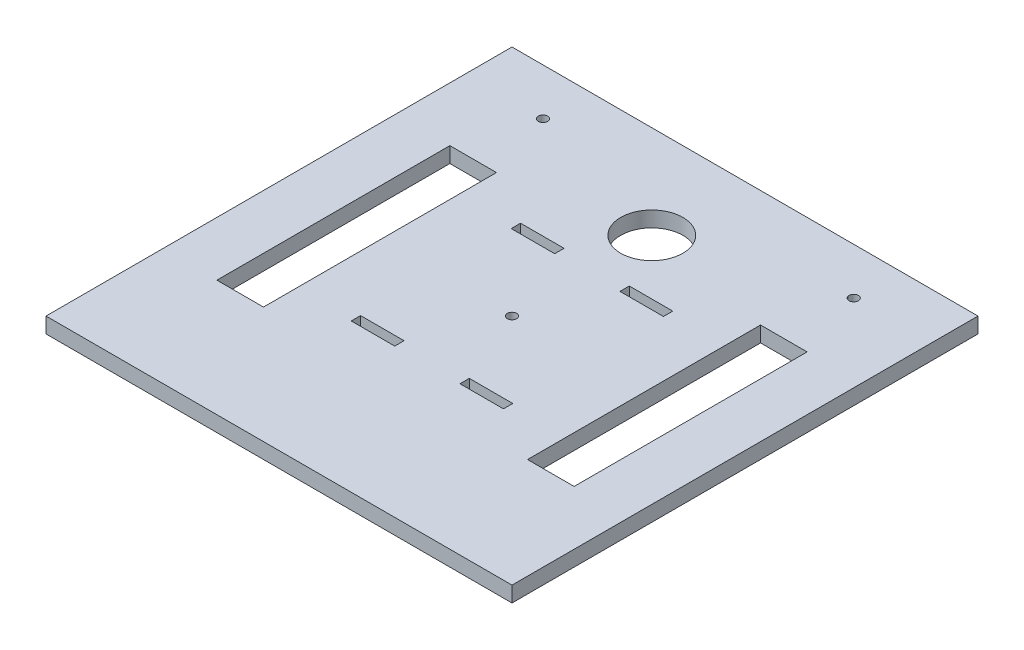
SolidWorks part; units mm, degrees
ref_plane "Front" through (0, 0, 0) normal (0, 0, 1) x (1, 0, 0)
ref_plane "Top" through (0, 0, 0) normal (0, 1, 0) x (1, 0, 0)
ref_plane "Right" through (0, 0, 0) normal (1, 0, 0) x (0, 0, -1)
sketch "Sketch1" plane through (0, 0, 0) normal (0, 1, 0) x (1, 0, 0)
  line L1 (75, -75) -> (-75, -75)
  line L2 (75, -75) -> (75, 75)
  line L3 (75, 75) -> (-75, 75)
  line L4 (-75, -75) -> (-75, 75)
  line L5 (0, 75) -> (0, -75) construction
  line L6 (75, 0) -> (-75, 0) construction
  line L7 (-57.5, -37.5) -> (-42.5, -37.5)
  line L8 (-57.5, -37.5) -> (-57.5, 37.5)
  line L9 (-57.5, 37.5) -> (-42.5, 37.5)
  line L10 (-42.5, -37.5) -> (-42.5, 37.5)
  line L11 (-50, 37.5) -> (-50, -37.5) construction
  line L12 (-57.5, 0) -> (-42.5, 0) construction
  line L13 (57.5, -37.5) -> (42.5, -37.5)
  line L14 (57.5, -37.5) -> (57.5, 37.5)
  line L15 (57.5, 37.5) -> (42.5, 37.5)
  line L16 (42.5, -37.5) -> (42.5, 37.5)
  line L17 (50, 37.5) -> (50, -37.5) construction
  line L18 (57.5, 0) -> (42.5, 0) construction
  point P0 (0, 0)
  point P4 (-50, 0)
  point P5 (50, 0)
  point P6 (-50, 0)
  point P10 (50, 0)
  dimension "D1" = 150
  dimension "D2" = 150
  dimension "D3" = 100
  dimension "D4" = 50
  dimension "D5" = 75
  dimension "D6" = 75
  dimension "D7" = 15
  dimension "D8" = 15
extrude "Boss-Extrude1" add sketch "Sketch1" along normal blind 5
sketch "Sketch2" plane through (0, 5, 0) normal (0, 1, 0) x (1, 0, 0)
  line L0 (-42.5, -37.5) -> (-42.5, 37.5) construction
  line L1 (17.5, -25.75) -> (-17.5, -25.75) construction
  line L2 (17.5, -25.75) -> (17.5, 25.75) construction
  line L3 (17.5, 25.75) -> (-17.5, 25.75) construction
  line L4 (-17.5, -25.75) -> (-17.5, 25.75) construction
  line L5 (0, 25.75) -> (0, -25.75) construction
  line L6 (17.5, 0) -> (-17.5, 0) construction
  line L7 (-10.5, 24.25) -> (-24.5, 24.25)
  line L8 (-10.5, 24.25) -> (-10.5, 27.25)
  line L9 (-10.5, 27.25) -> (-24.5, 27.25)
  line L10 (-24.5, 24.25) -> (-24.5, 27.25)
  line L11 (-17.5, 27.25) -> (-17.5, 24.25) construction
  line L12 (-10.5, 25.75) -> (-24.5, 25.75) construction
  line L13 (42.5, 37.5) -> (42.5, -37.5) construction
  line L14 (75, 75) -> (-75, 75) construction
  line L15 (24.5, 24.25) -> (10.5, 24.25)
  line L16 (24.5, 24.25) -> (24.5, 27.25)
  line L17 (24.5, 27.25) -> (10.5, 27.25)
  line L18 (10.5, 24.25) -> (10.5, 27.25)
  line L19 (17.5, 27.25) -> (17.5, 24.25) construction
  line L20 (24.5, 25.75) -> (10.5, 25.75) construction
  line L21 (-10.5, -27.25) -> (-24.5, -27.25)
  line L22 (-10.5, -27.25) -> (-10.5, -24.25)
  line L23 (-10.5, -24.25) -> (-24.5, -24.25)
  line L24 (-24.5, -27.25) -> (-24.5, -24.25)
  line L25 (-17.5, -24.25) -> (-17.5, -27.25) construction
  line L26 (-10.5, -25.75) -> (-24.5, -25.75) construction
  line L27 (10.5, -27.25) -> (24.5, -27.25)
  line L28 (10.5, -27.25) -> (10.5, -24.25)
  line L29 (10.5, -24.25) -> (24.5, -24.25)
  line L30 (24.5, -27.25) -> (24.5, -24.25)
  line L31 (17.5, -24.25) -> (17.5, -27.25) construction
  line L32 (10.5, -25.75) -> (24.5, -25.75) construction
  circle A0 centre (-50, 60) radius 1.5
  circle A1 centre (50, 60) radius 1.5
  circle A2 centre (0, 45) radius 10
  circle A3 centre (0, 0) radius 1.5
  point P0 (0, 0)
  dimension "D16" = 3
  dimension "D17" = 3
  dimension "D18" = 30
  dimension "D1" = 51.5
  dimension "D2" = 3
  dimension "D3" = 25
  dimension "D4" = 25
  dimension "D5" = 14
  dimension "D6" = 14
  dimension "D7" = 3
  dimension "D8" = 14
  dimension "D9" = 14
  dimension "D10" = 3
  dimension "D11" = 3
  dimension "D12" = 100
  dimension "D13" = 50
  dimension "D14" = 15
  dimension "D15" = 15
extrude "Cut-Extrude1" cut sketch "Sketch2" against normal blind 5
